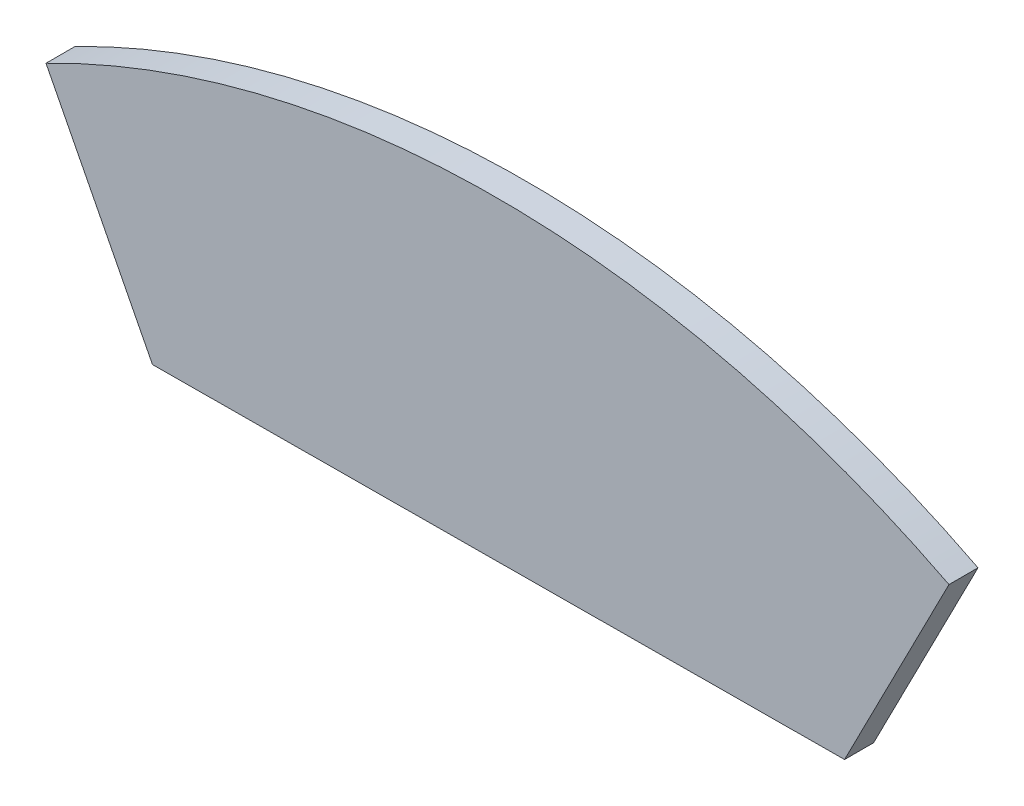
SolidWorks part; units mm, degrees
ref_plane "Front Plane" through (0, 0, 0) normal (0, 0, 1) x (1, 0, 0)
ref_plane "Top Plane" through (0, 0, 0) normal (0, 1, 0) x (1, 0, 0)
ref_plane "Right Plane" through (0, 0, 0) normal (1, 0, 0) x (0, 0, -1)
sketch "Sketch1" plane through (0, 0, 0) normal (0, 0, 1) x (1, 0, 0)
  line L0 (-49.3808, 96.3606) -> (-37.7376, 73.6402)
  line L2 (37.9612, 74.0765) -> (49.3808, 96.3606)
  line L3 (0, 0) -> (0, 132.1946) construction
  line L4 (0, -55) -> (0, 55) construction
  line L5 (-37.7376, 73.6402) -> (37.9612, 74.0765)
  arc A1 (49.3808, 96.3606) -> (-49.3808, 96.3606) centre (0, 0) ccw
  dimension "D1" = 25.53
  dimension "D2" = 75.7
extrude "Boss-Extrude1" add sketch "Sketch1" along normal blind 3.175
